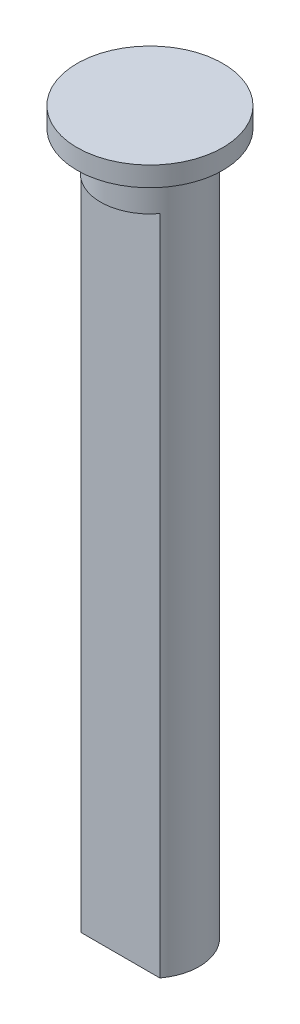
SolidWorks part; units mm, degrees
ref_plane "前视基准面" through (0, 0, 0) normal (0, 0, 1) x (1, 0, 0)
ref_plane "上视基准面" through (0, 0, 0) normal (0, 1, 0) x (1, 0, 0)
ref_plane "右视基准面" through (0, 0, 0) normal (1, 0, 0) x (0, 0, -1)
other "Configuration Table"
sketch "草图1" plane through (0, 0, 0) normal (0, 1, 0) x (1, 0, 0)
  line L0 (-2, -1.5) -> (2, -1.5)
  arc A0 (2, -1.5) -> (-2, -1.5) centre (0, 0) ccw
  dimension "D1" = 1.5
  dimension "D2" = 2.5
extrude "凸台-拉伸1" add sketch "草图1" along normal blind 27.8
sketch "草图2" plane through (0, 27.8, 0) normal (0, 1, 0) x (1, 0, 0)
  circle A0 centre (0, 0) radius 2.5
extrude "凸台-拉伸2" add sketch "草图2" along normal blind 2
sketch "草图3" plane through (0, 29.8, 0) normal (0, 1, 0) x (1, 0, 0)
  circle A0 centre (0, 0) radius 3.7
extrude "凸台-拉伸3" add sketch "草图3" along normal blind 1
sketch "草图4" plane through (0, 0, 0) normal (0, -1, 0) x (1, 0, 0)
  line L0 (-2, 1.5) -> (2, 1.5)
  arc A0 (-2, 1.5) -> (2, 1.5) centre (0, 0) ccw
extrude "凸台-拉伸4" add sketch "草图4" along normal blind 2
sketch "草图5" plane through (0, -2, 0) normal (0, -1, 0) x (1, 0, 0)
  line L0 (-2, 1.5) -> (2, 1.5)
  arc A0 (-2, 1.5) -> (2, 1.5) centre (0, 0) ccw
  dimension "D1" = 1.5
extrude "凸台-拉伸5" add sketch "草图5" along normal blind 3.8
